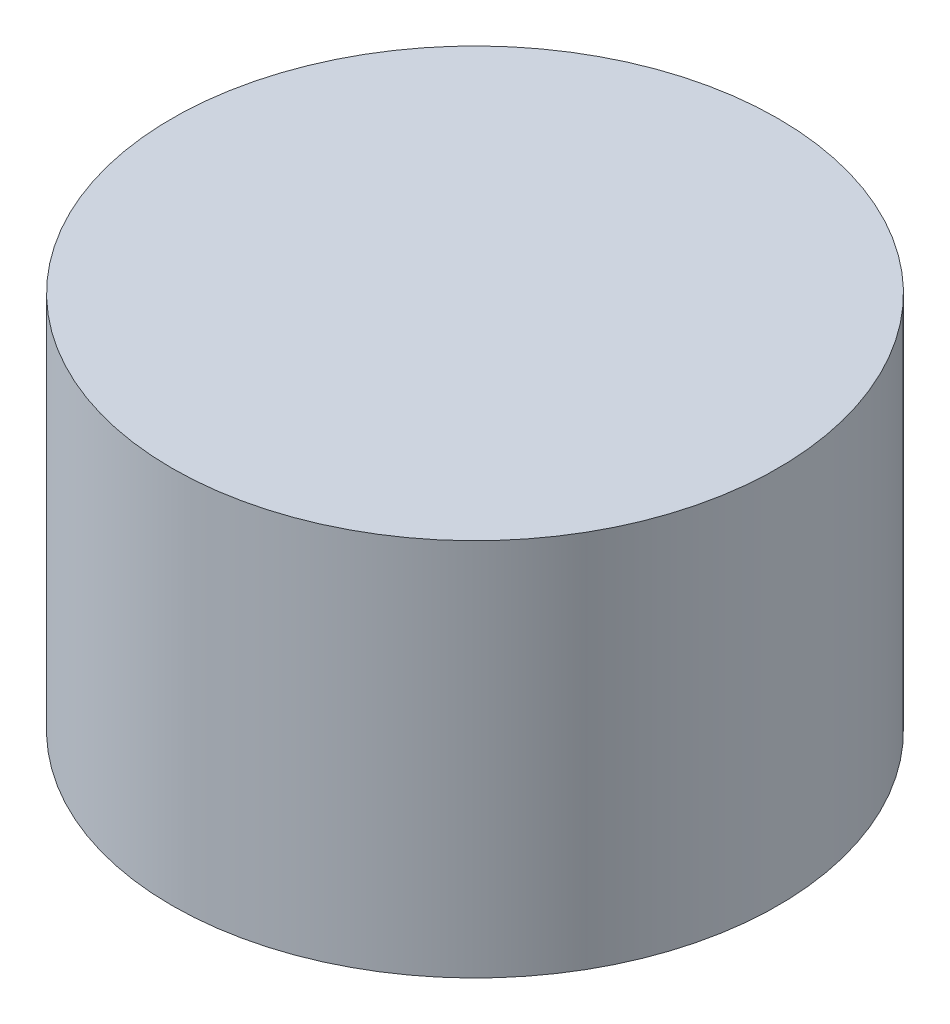
SolidWorks part; units mm, degrees
ref_plane "Front Plane" through (0, 0, 0) normal (0, 0, 1) x (1, 0, 0)
ref_plane "Top Plane" through (0, 0, 0) normal (0, 1, 0) x (1, 0, 0)
ref_plane "Right Plane" through (0, 0, 0) normal (1, 0, 0) x (0, 0, -1)
sketch "Sketch1" plane through (0, 0, 0) normal (0, 1, 0) x (1, 0, 0)
  circle A0 centre (0, 0) radius 40
extrude "Boss-Extrude1" add sketch "Sketch1" along normal blind 50 contours A0
